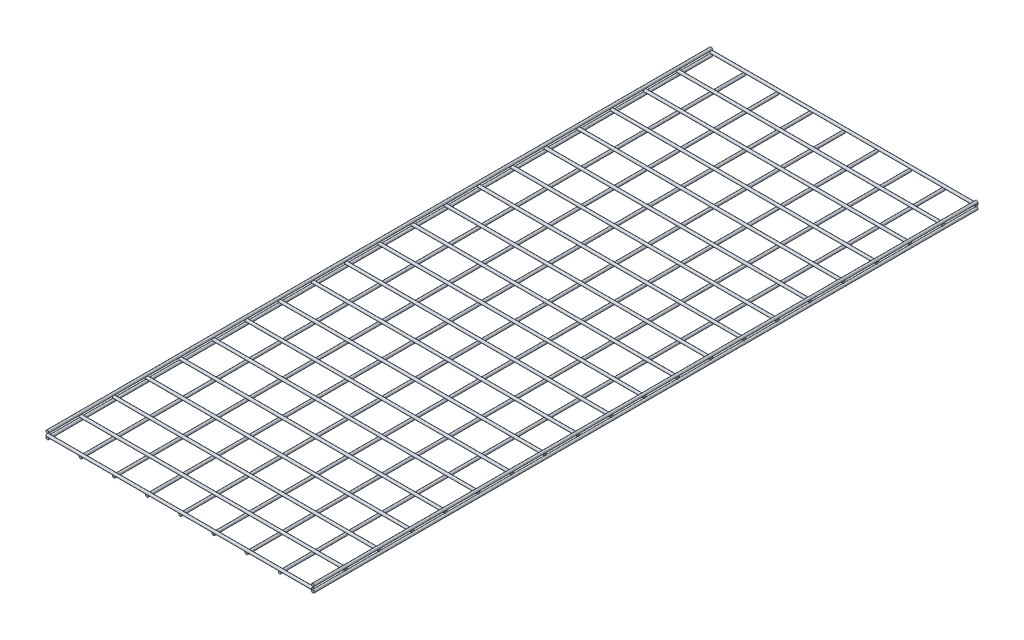
SolidWorks part; units mm, degrees
material "Plain Carbon Steel"
ref_plane "Front Plane" through (0, 0, 0) normal (0, 0, 1) x (1, 0, 0)
ref_plane "Top Plane" through (0, 0, 0) normal (0, 1, 0) x (1, 0, 0)
ref_plane "Right Plane" through (0, 0, 0) normal (1, 0, 0) x (0, 0, -1)
sketch "Sketch1" plane through (0, 0, 0) normal (0, 0, 1) x (1, 0, 0)
  line L0 (0, -55) -> (0, 55) construction
  circle A0 centre (0, 0) radius 3.175
  circle A1 centre (0, 12.7) radius 3.175
  circle A2 centre (76.2, 0) radius 3.175
  circle A3 centre (152.4, 0) radius 3.175
  circle A4 centre (228.6, 0) radius 3.175
  circle A5 centre (304.8, 0) radius 3.175
  circle A6 centre (381, 0) radius 3.175
  circle A7 centre (457.2, 0) radius 3.175
  circle A8 centre (533.4, 0) radius 3.175
  circle A9 centre (609.6, 0) radius 3.175
  circle A10 centre (609.6, 12.7) radius 3.175
  dimension "D1" = 6.35
  dimension "D2" = 6.35
  dimension "D6" = 6.35
  dimension "D3" = 12.7
  dimension "D5" = 12.7
  dimension "D4" = 9
extrude "Boss-Extrude1" add sketch "Sketch1" along normal blind 1524
sketch "Sketch2" plane through (0, 0, 0) normal (1, 0, 0) x (0, 0, -1)
  line L0 (0, 15.875) -> (-1524, 15.875) construction
  line L1 (0, 10.4775) -> (0, -10.4775) construction
  circle A0 centre (0, 6.35) radius 3.175
  circle A1 centre (-76.2, 6.35) radius 3.175
  circle A2 centre (-152.4, 6.35) radius 3.175
  circle A3 centre (-228.6, 6.35) radius 3.175
  circle A4 centre (-304.8, 6.35) radius 3.175
  circle A5 centre (-381, 6.35) radius 3.175
  circle A6 centre (-457.2, 6.35) radius 3.175
  circle A7 centre (-533.4, 6.35) radius 3.175
  circle A8 centre (-609.6, 6.35) radius 3.175
  circle A9 centre (-685.8, 6.35) radius 3.175
  circle A10 centre (-762, 6.35) radius 3.175
  circle A11 centre (-838.2, 6.35) radius 3.175
  circle A12 centre (-914.4, 6.35) radius 3.175
  circle A13 centre (-990.6, 6.35) radius 3.175
  circle A14 centre (-1066.8, 6.35) radius 3.175
  circle A15 centre (-1143, 6.35) radius 3.175
  circle A16 centre (-1219.2, 6.35) radius 3.175
  circle A17 centre (-1295.4, 6.35) radius 3.175
  circle A18 centre (-1371.6, 6.35) radius 3.175
  circle A19 centre (-1447.8, 6.35) radius 3.175
  circle A20 centre (-1524, 6.35) radius 3.175
  dimension "D2" = 6.35
  dimension "D1" = 9.525
  dimension "D3" = 0
  dimension "D4" = 21
extrude "Boss-Extrude2" add sketch "Sketch2" along normal blind 609.6 separate body
